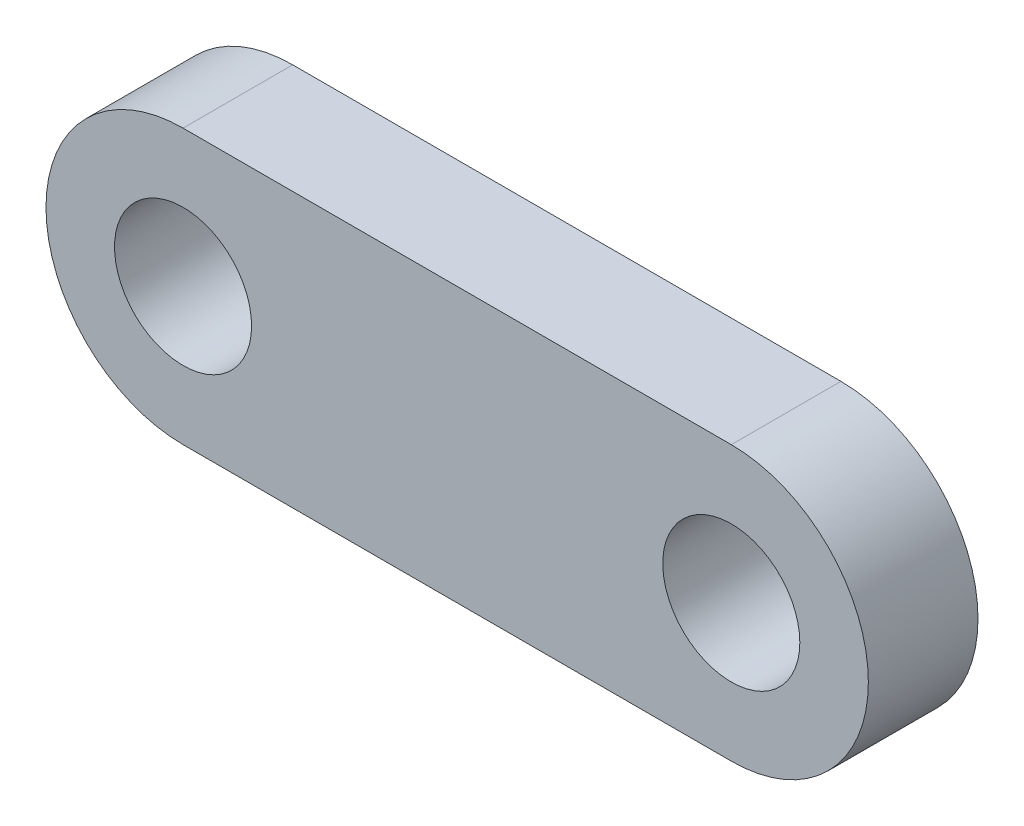
SolidWorks part; units mm, degrees
ref_plane "Front Plane" through (0, 0, 0) normal (0, 0, 1) x (1, 0, 0)
ref_plane "Top Plane" through (0, 0, 0) normal (0, 1, 0) x (1, 0, 0)
ref_plane "Right Plane" through (0, 0, 0) normal (1, 0, 0) x (0, 0, -1)
sketch "Sketch1" plane through (0, 0, 0) normal (0, 0, 1) x (1, 0, 0)
  line L0 (-12.7, 0) -> (12.7, 0) construction
  line L1 (-12.7, 6.35) -> (12.7, 6.35)
  line L2 (-12.7, -6.35) -> (12.7, -6.35)
  arc A0 (-12.7, 6.35) -> (-12.7, -6.35) centre (-12.7, 0) ccw
  arc A1 (12.7, -6.35) -> (12.7, 6.35) centre (12.7, 0) ccw
  circle A2 centre (-12.7, 0) radius 3.175
  circle A3 centre (12.7, 0) radius 3.175
  point P2 (0, 0)
  dimension "D1" = 6.35
  dimension "D3" = 6.35
  dimension "D2" = 25.4
extrude "Boss-Extrude1" add sketch "Sketch1" along normal blind 5.08
